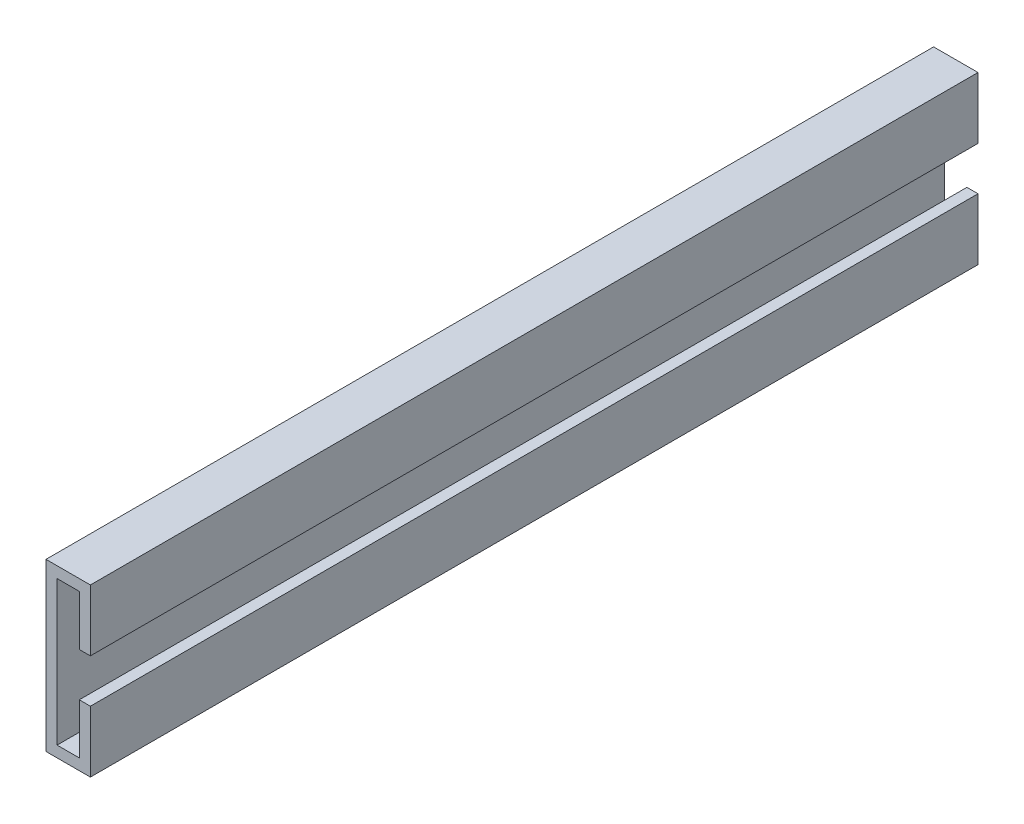
SolidWorks part; units mm, degrees
ref_plane "Front Plane" through (0, 0, 0) normal (0, 0, 1) x (1, 0, 0)
ref_plane "Top Plane" through (0, 0, 0) normal (0, 1, 0) x (1, 0, 0)
ref_plane "Right Plane" through (0, 0, 0) normal (1, 0, 0) x (0, 0, -1)
sketch "Sketch1" plane through (0, 0, 0) normal (0, 0, 1) x (1, 0, 0)
  line L0 (0, -65) -> (0, 65)
  line L1 (0, 65) -> (20, 65)
  line L2 (20, 65) -> (20, 19.6423)
  line L3 (20, 19.6423) -> (30, 19.6423)
  line L4 (30, 19.6423) -> (30, 75)
  line L5 (30, 75) -> (-10, 75)
  line L6 (55, 0) -> (-55, 0) construction
  line L7 (30, -75) -> (-10, -75)
  line L8 (30, -19.6423) -> (30, -75)
  line L9 (20, -19.6423) -> (30, -19.6423)
  line L10 (20, -65) -> (20, -19.6423)
  line L11 (0, -65) -> (20, -65)
  line L12 (-10, 75) -> (-10, -75)
  point P19 (0, 0)
extrude "Boss-Extrude1" add sketch "Sketch1" along normal mid plane 800
